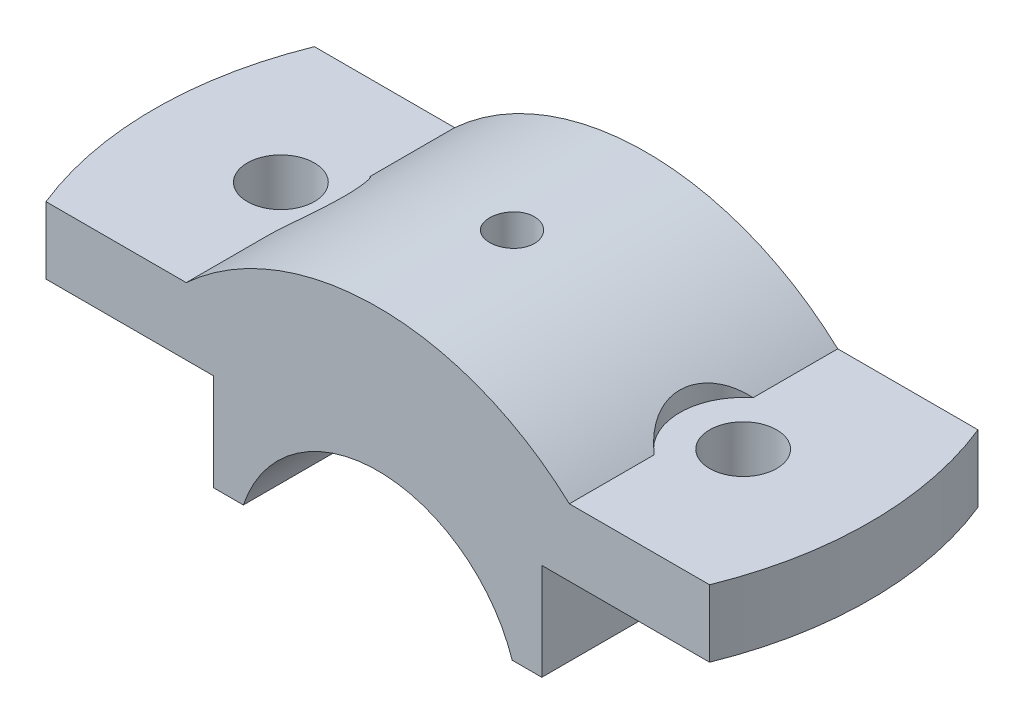
SolidWorks part; units mm, degrees
ref_plane "Front Plane" through (0, 0, 0) normal (0, 0, 1) x (1, 0, 0)
ref_plane "Top Plane" through (0, 0, 0) normal (0, 1, 0) x (1, 0, 0)
ref_plane "Right Plane" through (0, 0, 0) normal (1, 0, 0) x (0, 0, -1)
sketch "Sketch1" plane through (0, 0, 0) normal (0, 0, 1) x (1, 0, 0)
  line L0 (0, 0) -> (0, 63.3657) construction
  line L1 (18.0278, 6) -> (22, 6)
  line L2 (22, 6) -> (22, 19)
  line L3 (22, 19) -> (50, 19)
  line L4 (50, 19) -> (50, 28)
  line L5 (50, 28) -> (25.6905, 28)
  line L6 (-18.0278, 6) -> (-22, 6)
  line L7 (-22, 6) -> (-22, 19)
  line L8 (-22, 19) -> (-50, 19)
  line L9 (-50, 19) -> (-50, 28)
  line L10 (-50, 28) -> (-25.6905, 28)
  arc A0 (25.6905, 28) -> (-25.6905, 28) centre (0, 0) ccw
  arc A1 (18.0278, 6) -> (-18.0278, 6) centre (0, 0) ccw
  dimension "D1" = 19
  dimension "D3" = 38
  dimension "D2" = 44
  dimension "D4" = 6
  dimension "D5" = 19
  dimension "D6" = 9
  dimension "D7" = 50
extrude "Boss-Extrude1" add sketch "Sketch1" along normal mid plane 36
sketch "Sketch2" plane through (0, 0, 0) normal (0, 1, 0) x (1, 0, 0)
  line L0 (-25.6905, 18) -> (-50, 18) construction
  line L1 (-44.4972, 18) -> (-50, 18)
  line L2 (-50, -18) -> (-50, 18) construction
  line L3 (-25.6905, -18) -> (-50, -18) construction
  line L4 (-50, -18) -> (-50, 18)
  line L5 (-44.4972, -18) -> (-50, -18)
  arc A0 (-44.4972, 18) -> (-44.4972, -18) centre (0, 0) ccw
  dimension "D1" = 48
extrude "Cut-Extrude1" cut sketch "Sketch2" along normal through all
sketch "Sketch3" plane through (0, 28, 0) normal (0, 1, 0) x (1, 0, 0)
  circle A0 centre (-31, 0) radius 4.5
  dimension "D1" = 9
  dimension "D2" = 31
extrude "Cut-Extrude2" cut sketch "Sketch3" against normal blind 58
sketch "Sketch4" plane through (0, 28, 0) normal (0, 1, 0) x (1, 0, 0)
  line L0 (-25.6905, -18) -> (-25.6905, 18) construction
  line L1 (-25.6905, -6.6377) -> (-25.6905, 6.6377)
  arc A0 (-25.6905, -6.6377) -> (-25.6905, 6.6377) centre (-31, 0) ccw
  dimension "D1" = 8.5
extrude "Cut-Extrude3" cut sketch "Sketch4" along normal blind 64
mirror "Mirror5" about plane through (0, 0, 0) normal (1, 0, 0) of "Cut-Extrude3", "Cut-Extrude2", "Cut-Extrude1"
hole_wizard "CBORE for M5 Hex Head Bolt1" positions "3DSketch1" profile "Sketch7" counterbore size "M5" standard "ANSI Metric" end condition through all
sketch3d "3DSketch1"
  point P0 (0, 38, 0)
  point P3 (0, 38, 0)
  dimension "D1" = 0
  dimension "D2" = 0
sketch "Sketch7" plane through (0, 38, 0) normal (1, 0, 0) x (0, 0, 1)
  line L0 (0, 0) -> (0, 32)
  line L1 (0, 32) -> (2.5, 32)
  line L2 (2.5, 13.495) -> (2.5, 32)
  line L3 (2.5, 13.495) -> (2.995, 13)
  line L4 (2.995, 13) -> (3, 13)
  line L5 (3, 13) -> (3, 0)
  line L7 (0, 0) -> (3, 0)
  line L9 (-2.5, 13.495) -> (-2.995, 13) construction
  line L11 (0, -6.35) -> (0, 107.95) construction
  dimension "Thru Hole Dia." = 5
  dimension "Thru Hole Depth" = 32
  dimension "C'Bore Dia." = 6
  dimension "C'Bore Depth" = 13
  dimension "Mid C'Sink Dia." = 5.99
  dimension "Mid C'Sink Angle" = 90
